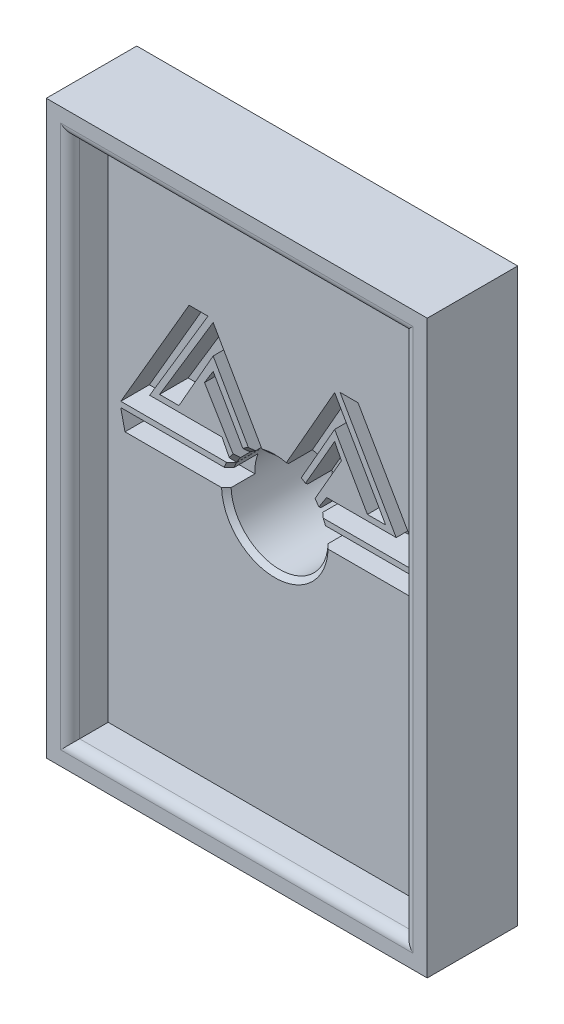
SolidWorks part; units mm, degrees
ref_plane "Front Plane" through (0, 0, 0) normal (0, 0, 1) x (1, 0, 0)
ref_plane "Top Plane" through (0, 0, 0) normal (0, 1, 0) x (1, 0, 0)
ref_plane "Right Plane" through (0, 0, 0) normal (1, 0, 0) x (0, 0, -1)
sketch "Sketch1" plane through (0, 0, 0) normal (0, 0, 1) x (1, 0, 0)
  line L1 (-10, -15) -> (10, -15)
  line L2 (-10, -15) -> (-10, 15)
  line L3 (-10, 15) -> (10, 15)
  line L4 (10, -15) -> (10, 15)
  line L5 (-10, -15) -> (10, 15) construction
  line L6 (-10, 15) -> (10, -15) construction
  point P0 (0, 0)
  dimension "D1" = 30
  dimension "D2" = 20
extrude "Boss-Extrude1" add sketch "Sketch1" along normal blind 5
sketch "Sketch4" plane through (0, 0, 0) normal (0, 0, -1) x (-1, 0, 0)
  line L1 (-5.75, -9.75) -> (5.75, -9.75)
  line L2 (-5.75, -9.75) -> (-5.75, 9.75)
  line L3 (-5.75, 9.75) -> (5.75, 9.75)
  line L4 (5.75, -9.75) -> (5.75, 9.75)
  line L5 (-5.75, -9.75) -> (5.75, 9.75) construction
  line L6 (-5.75, 9.75) -> (5.75, -9.75) construction
  point P0 (0, 0)
  dimension "D1" = 19.5
  dimension "D2" = 11.5
extrude "Boss-Extrude2" add sketch "Sketch4" along normal blind 2.5
sketch "Sketch2" plane through (0, 0, 5) normal (0, 0, 1) x (1, 0, 0)
  line L0 (0, 15) -> (0, -15) construction
  line L1 (10, 15) -> (-10, 15) construction
  line L2 (-10, -15) -> (10, -15) construction
  circle A0 centre (0, 0) radius 2.55
  dimension "D1" = 5.1
extrude "Cut-Extrude1" cut sketch "Sketch2" against normal through all
sketch "Sketch3" plane through (0, 0, 5) normal (0, 0, 1) x (1, 0, 0)
  line L1 (-8.75, -13.75) -> (8.75, -13.75)
  line L2 (-8.75, -13.75) -> (-8.75, 13.75)
  line L3 (-8.75, 13.75) -> (8.75, 13.75)
  line L4 (8.75, -13.75) -> (8.75, 13.75)
  line L5 (-8.75, -13.75) -> (8.75, 13.75) construction
  line L6 (-8.75, 13.75) -> (8.75, -13.75) construction
  point P0 (0, 0)
  dimension "D1" = 27.5
  dimension "D2" = 17.5
extrude "Cut-Extrude2" cut sketch "Sketch3" against normal blind 2
fillet "Fillet1" radius 0.5 5 edges at (0, -9.75, -2.5) (5.75, 0, -2.5) (0, 9.75, -2.5) (-5.75, 0, -2.5) (2.55, 0, -2.5)
chamfer "Chamfer1" distance 0.25 angle 45 8 edges at (5.75, 0, 0) (0, -9.75, 0) (-5.75, 0, 0) (0, 9.75, 0) (0, 15, 0) (-10, 0, 0) (0, -15, 0) (10, 0, 0)
chamfer "Chamfer2" distance 0.25 angle 45 1 edges at (-2.55, 0, 3)
fillet "Fillet2" radius 0.5 4 edges at (0, -13.75, 5) (8.75, 0, 5) (0, 13.75, 5) (-8.75, 0, 5)
ref_plane "Plane1" through (0, 0, 5) normal (0, 0, 1) x (1, 0, 0)
sketch "Mobious Logo" plane through (0, 0, 5) normal (0, 0, 1) x (-1, 0, 0)
  line L0 (3.5092, -7.3382) -> (4.5022, -7.3382)
  line L1 (4.5022, -7.3382) -> (8.0873, -1.178)
  line L2 (8.0873, -1.178) -> (2.2469, -1.178)
  line L3 (2.2469, -1.178) -> (2.7733, -2.2087)
  line L4 (2.7733, -2.2087) -> (6.5725, -2.2087)
  line L5 (6.5725, -2.2087) -> (3.5092, -7.3382)
  line L6 (3.6943, -4.2244) -> (3.2399, -4.965)
  line L7 (3.2399, -4.965) -> (0.3449, 0.1012)
  line L8 (0.3449, 0.1012) -> (7.8685, 0.1012)
  line L9 (7.8685, 0.1012) -> (8.091, -0.8919)
  line L10 (8.091, -0.8919) -> (1.6847, -0.8919)
  line L11 (1.6847, -0.8919) -> (3.6943, -4.2244)
  line L12 (6.0507, -2.5077) -> (3.2399, -7.1867)
  line L13 (3.2399, -7.1867) -> (0.042, -1.5984)
  line L14 (0.042, -1.5984) -> (-3.1391, -7.1867)
  line L15 (-3.1391, -7.1867) -> (-5.8167, -2.5077)
  line L16 (-5.8167, -2.5077) -> (-4.8599, -2.5077)
  line L17 (-4.8599, -2.5077) -> (-3.1391, -5.5146)
  line L18 (-3.1391, -5.5146) -> (0, 0)
  line L19 (0, 0) -> (3.2399, -5.6617)
  line L20 (3.2399, -5.6617) -> (5.0353, -2.5077)
  line L21 (5.0353, -2.5077) -> (6.0507, -2.5077)
  line L22 (-3.4253, -7.3382) -> (-4.3678, -7.3382)
  line L23 (-4.3678, -7.3382) -> (-7.9192, -1.178)
  line L24 (-7.9192, -1.178) -> (-2.0619, -1.178)
  line L25 (-2.0619, -1.178) -> (-2.7183, -2.2087)
  line L26 (-2.7183, -2.2087) -> (-6.3707, -2.2087)
  line L27 (-6.3707, -2.2087) -> (-3.4253, -7.3382)
  line L28 (-3.1391, -4.965) -> (-0.2273, 0.1012)
  line L29 (-0.2273, 0.1012) -> (-7.6499, 0.1012)
  line L30 (-7.6499, 0.1012) -> (-8.0437, -0.8919)
  line L31 (-8.0437, -0.8919) -> (-1.557, -0.8919)
  line L32 (-1.557, -0.8919) -> (-3.4941, -4.2622)
  line L33 (-3.4941, -4.2622) -> (-3.1391, -4.965)
extrude "Cut-Extrude5" cut sketch "Mobious Logo" against normal blind 3.5
